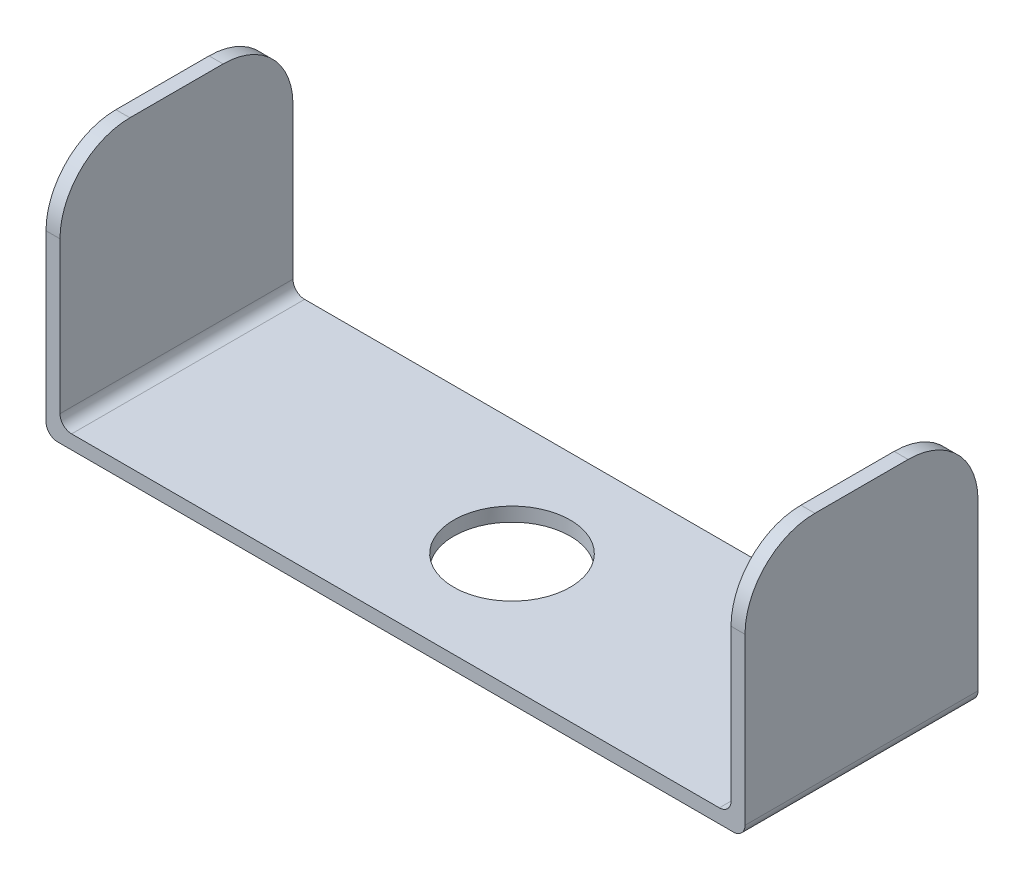
SolidWorks part; units mm, degrees
ref_plane "Front Plane" through (0, 0, 0) normal (0, 0, 1) x (1, 0, 0)
ref_plane "Top Plane" through (0, 0, 0) normal (0, 1, 0) x (1, 0, 0)
ref_plane "Right Plane" through (0, 0, 0) normal (1, 0, 0) x (0, 0, -1)
sketch "Sketch1" plane through (0, 0, 0) normal (0, 1, 0) x (1, 0, 0)
  line L1 (-15, -5) -> (15, -5)
  line L2 (-15, -5) -> (-15, 5)
  line L3 (-15, 5) -> (15, 5)
  line L4 (15, -5) -> (15, 5)
  line L5 (-15, -5) -> (15, 5) construction
  line L6 (-15, 5) -> (15, -5) construction
  point P0 (0, 0)
  dimension "D1" = 30
  dimension "D2" = 10
extrude "Boss-Extrude1" add sketch "Sketch1" along normal blind 0.6
sketch "Sketch2" plane through (0, 0.6, 0) normal (0, 1, 0) x (1, 0, 0)
  line L0 (-15, -5) -> (15, -5) construction
  line L1 (-15, 5) -> (-14.4, 5)
  line L2 (-15, 5) -> (-15, -5)
  line L3 (-15, -5) -> (-14.4, -5)
  line L4 (-14.4, 5) -> (-14.4, -5)
  line L6 (15, 5) -> (14.4, 5)
  line L7 (15, 5) -> (15, -5)
  line L8 (15, -5) -> (14.4, -5)
  line L9 (14.4, 5) -> (14.4, -5)
  dimension "D1" = 0.6
  dimension "D2" = 0.6
extrude "Boss-Extrude2" add sketch "Sketch2" along normal blind 10
fillet "Fillet1" radius 0.5 4 edges at (15, 0, 0) (14.4, 0.6, 0) (-15, 0, 0) (-14.4, 0.6, 0)
fillet "Fillet2" radius 3 4 edges at (-14.7, 10.6, -5) (-14.7, 10.6, 5) (14.7, 10.6, -5) (14.7, 10.6, 5)
sketch "Sketch3" plane through (0, 0.6, 0) normal (0, 1, 0) x (1, 0, 0)
  circle A0 centre (0, 0) radius 2.5
  dimension "D1" = 5
extrude "Cut-Extrude1" cut sketch "Sketch3" against normal up to next
